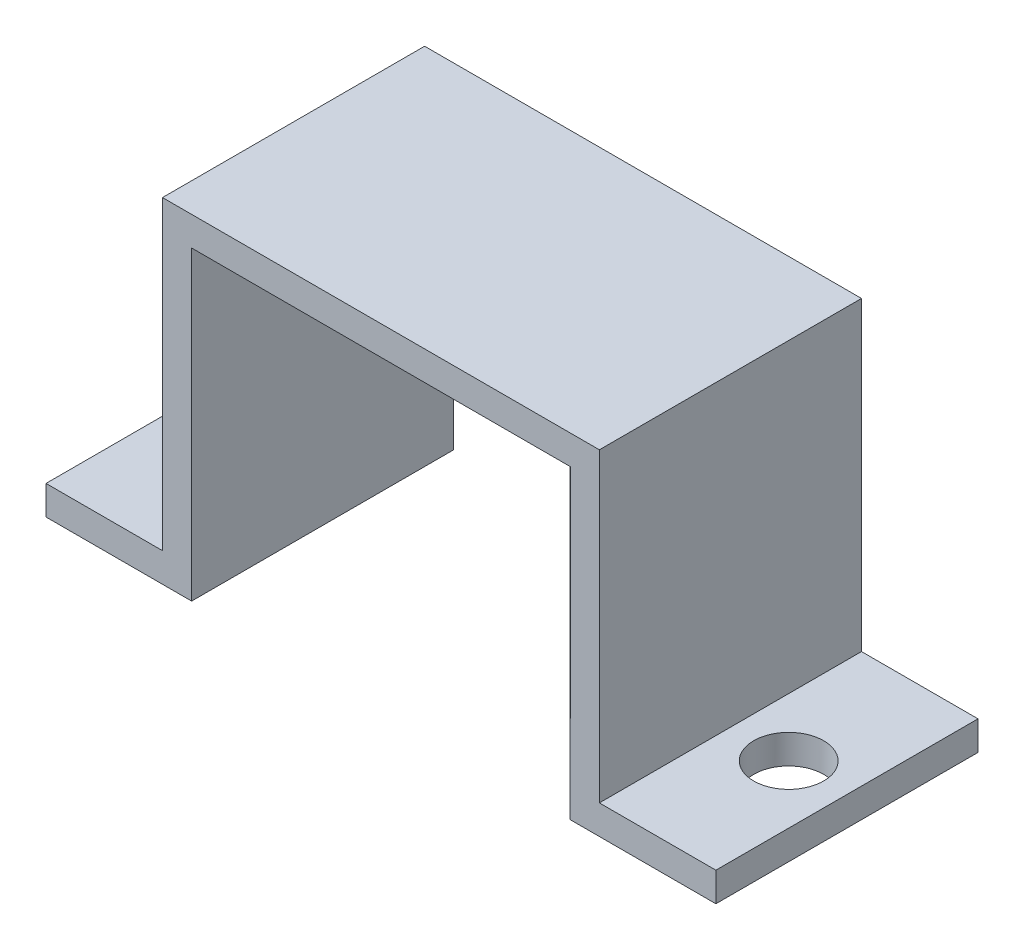
SolidWorks part; units mm, degrees
ref_plane "Front Plane" through (0, 0, 0) normal (0, 0, 1) x (1, 0, 0)
ref_plane "Top Plane" through (0, 0, 0) normal (0, 1, 0) x (1, 0, 0)
ref_plane "Right Plane" through (0, 0, 0) normal (1, 0, 0) x (0, 0, -1)
sketch "Sketch1" plane through (0, 0, 0) normal (0, 0, 1) x (1, 0, 0)
  line L0 (0, 0) -> (0, 3.3181)
  line L1 (-6.5, 0) -> (-6.5, 10.5)
  line L2 (-6.5, 0) -> (-11.5, 0)
  line L3 (-11.5, 0) -> (-11.5, 1)
  line L4 (-11.5, 1) -> (-7.5, 1)
  line L5 (-7.5, 1) -> (-7.5, 11.5)
  line L6 (7.5, 1) -> (7.5, 11.5)
  line L7 (11.5, 1) -> (7.5, 1)
  line L8 (11.5, 0) -> (11.5, 1)
  line L9 (6.5, 0) -> (11.5, 0)
  line L10 (6.5, 0) -> (6.5, 10.5)
  line L11 (-6.5, 10.5) -> (6.5, 10.5)
  line L12 (7.5, 11.5) -> (-7.5, 11.5)
extrude "Boss-Extrude1" add sketch "Sketch1" along normal blind 9 contours L6 L12 L5 L4 L3 L2 L1 L11 L10 L9 L8 L7
sketch "Sketch2" plane through (0, 1, 0) normal (0, 1, 0) x (1, 0, 0)
  circle A0 centre (9.5, -4.5) radius 1.2
extrude "Cut-Extrude1" cut sketch "Sketch2" against normal blind 29
mirror "Mirror1" about plane through (0, 0, 0) normal (1, 0, 0) of "Cut-Extrude1"
